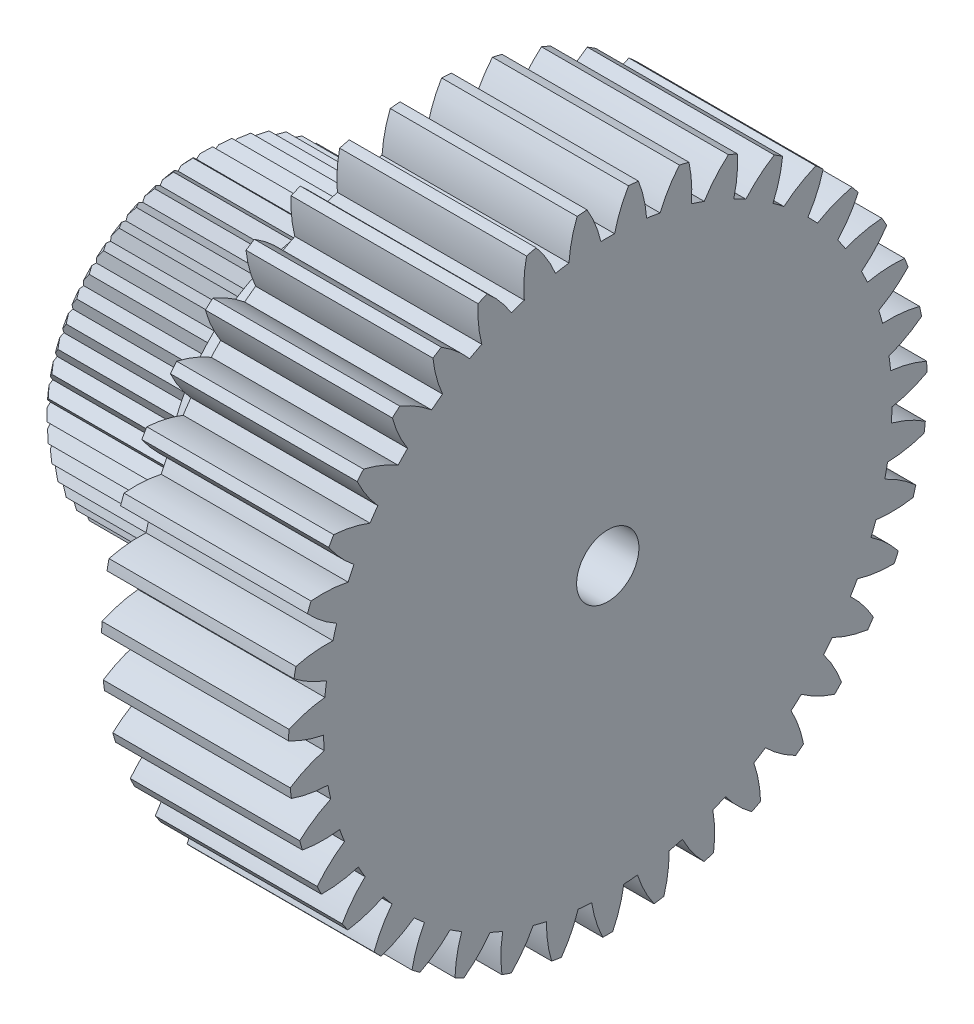
SolidWorks part; units mm, degrees
ref_plane "Plan de face" through (0, 0, 0) normal (0, 0, 1) x (1, 0, 0)
ref_plane "Plan de dessus" through (0, 0, 0) normal (0, 1, 0) x (1, 0, 0)
ref_plane "Plan de droite" through (0, 0, 0) normal (1, 0, 0) x (0, 0, -1)
ref_plane "Plan1" through (0, 0, 0) normal (0, 0, -1) x (-1, 0, 0)
sketch "Esquisse1" plane through (0, 0, 0) normal (0, 0, -1) x (-1, 0, 0)
  line L0 (-3, 5.125) -> (-3, 0)
  line L1 (-3, 0) -> (0, 0)
  line L2 (0, 0) -> (0, 5.125)
  line L3 (0, 5.125) -> (-3, 5.125)
  line L4 (-3, 0) -> (0, 0) construction
revolve "Révolution1" add sketch "Esquisse1" angle 360 about L4
sketch "Esquisse2" plane through (3, 0, 0) normal (1, 0, 0) x (0, 0, -1)
  arc A0 (1.9354, 4.7455) -> (1.3036, 4.9564) centre (0, 0) ccw
  arc A1 (1.3036, 4.9564) -> (1.3398, 4.3603) centre (-0.6017, 4.5413) cw
  arc A2 (1.3398, 4.3603) -> (1.5483, 4.2907) centre (0, 0) cw
  arc A3 (1.5483, 4.2907) -> (1.9354, 4.7455) centre (3.2092, 3.269) cw
extrude "Enlèv. mat.-Extru.1" cut sketch "Esquisse2" against normal through all
sketch "Esquisse3" plane through (3, 0, 0) normal (1, 0, 0) x (0, 0, -1)
  arc A0 (2.6716, 4.3736) -> (2.0817, 4.6832) centre (0, 0) ccw
  arc A1 (2.0817, 4.6832) -> (2.0219, 4.0889) centre (0.1345, 4.579) cw
  arc A2 (2.0219, 4.0889) -> (2.2165, 3.9868) centre (0, 0) cw
  arc A3 (2.2165, 3.9868) -> (2.6716, 4.3736) centre (3.692, 2.7119) cw
extrude "Enlèv. mat.-Extru.2" cut sketch "Esquisse3" against normal through all
sketch "Esquisse4" plane through (3, 0, 0) normal (1, 0, 0) x (0, 0, -1)
  arc A0 (3.3386, 3.8884) -> (2.806, 4.2886) centre (0, 0) ccw
  arc A1 (2.806, 4.2886) -> (2.6516, 3.7116) centre (0.8673, 4.4981) cw
  arc A2 (2.6516, 3.7116) -> (2.8273, 3.5796) centre (0, 0) cw
  arc A3 (2.8273, 3.5796) -> (3.3386, 3.8884) centre (4.0793, 2.0845) cw
extrude "Enlèv. mat.-Extru.3" cut sketch "Esquisse4" against normal through all
sketch "Esquisse5" plane through (3, 0, 0) normal (1, 0, 0) x (0, 0, -1)
  arc A0 (3.9191, 3.3025) -> (3.4576, 3.7829) centre (0, 0) ccw
  arc A1 (3.4576, 3.7829) -> (3.2127, 3.2382) centre (1.5776, 4.3008) cw
  arc A2 (3.2127, 3.2382) -> (3.3649, 3.0797) centre (0, 0) cw
  arc A3 (3.3649, 3.0797) -> (3.9191, 3.3025) centre (4.3608, 1.4032) cw
extrude "Enlèv. mat.-Extru.4" cut sketch "Esquisse5" against normal through all
sketch "Esquisse6" plane through (3, 0, 0) normal (1, 0, 0) x (0, 0, -1)
  arc A0 (4.3981, 2.6311) -> (4.0197, 3.1793) centre (0, 0) ccw
  arc A1 (4.0197, 3.1793) -> (3.6905, 2.6809) centre (2.2471, 3.992) cw
  arc A2 (3.6905, 2.6809) -> (3.8154, 2.5) centre (0, 0) cw
  arc A3 (3.8154, 2.5) -> (4.3981, 2.6311) centre (4.5294, 0.6855) cw
extrude "Enlèv. mat.-Extru.5" cut sketch "Esquisse6" against normal through all
sketch "Esquisse7" plane through (3, 0, 0) normal (1, 0, 0) x (0, 0, -1)
  arc A0 (4.7632, 1.8915) -> (4.4776, 2.4933) centre (0, 0) ccw
  arc A1 (4.4776, 2.4933) -> (4.0728, 2.0542) centre (2.8584, 3.5799) cw
  arc A2 (4.0728, 2.0542) -> (4.167, 1.8556) centre (0, 0) cw
  arc A3 (4.167, 1.8556) -> (4.7632, 1.8915) centre (4.5807, -0.05) cw
extrude "Enlèv. mat.-Extru.6" cut sketch "Esquisse7" against normal through all
sketch "Esquisse8" plane through (3, 0, 0) normal (1, 0, 0) x (0, 0, -1)
  arc A0 (5.0049, 1.1029) -> (4.8196, 1.7428) centre (0, 0) ccw
  arc A1 (4.8196, 1.7428) -> (4.3496, 1.3743) centre (3.3956, 3.075) cw
  arc A2 (4.3496, 1.3743) -> (4.4107, 1.1632) centre (0, 0) cw
  arc A3 (4.4107, 1.1632) -> (5.0049, 1.1029) centre (4.5134, -0.7841) cw
extrude "Enlèv. mat.-Extru.7" cut sketch "Esquisse8" against normal through all
sketch "Esquisse9" plane through (3, 0, 0) normal (1, 0, 0) x (0, 0, -1)
  arc A0 (5.117, 0.2858) -> (5.0367, 0.9471) centre (0, 0) ccw
  arc A1 (5.0367, 0.9471) -> (4.5137, 0.6588) centre (3.8449, 2.4905) cw
  arc A2 (4.5137, 0.6588) -> (4.5402, 0.4406) centre (0, 0) cw
  arc A3 (4.5402, 0.4406) -> (5.117, 0.2858) centre (4.3292, -1.498) cw
extrude "Enlèv. mat.-Extru.8" cut sketch "Esquisse9" against normal through all
sketch "Esquisse10" plane through (3, 0, 0) normal (1, 0, 0) x (0, 0, -1)
  arc A0 (5.0966, -0.5387) -> (5.1234, 0.1269) centre (0, 0) ccw
  arc A1 (5.1234, 0.1269) -> (4.5609, -0.0738) centre (4.1946, 1.8415) cw
  arc A2 (4.5609, -0.0738) -> (4.5521, -0.2934) centre (0, 0) cw
  arc A3 (4.5521, -0.2934) -> (5.0966, -0.5387) centre (4.0328, -2.173) cw
extrude "Enlèv. mat.-Extru.9" cut sketch "Esquisse10" against normal through all
sketch "Esquisse11" plane through (3, 0, 0) normal (1, 0, 0) x (0, 0, -1)
  arc A0 (4.9442, -1.3493) -> (5.0774, -0.6966) centre (0, 0) ccw
  arc A1 (5.0774, -0.6966) -> (4.49, -0.8045) centre (4.4357, 1.1448) cw
  arc A2 (4.49, -0.8045) -> (4.446, -1.0198) centre (0, 0) cw
  arc A3 (4.446, -1.0198) -> (4.9442, -1.3493) centre (3.632, -2.7918) cw
extrude "Enlèv. mat.-Extru.10" cut sketch "Esquisse11" against normal through all
sketch "Esquisse12" plane through (3, 0, 0) normal (1, 0, 0) x (0, 0, -1)
  arc A0 (4.6637, -2.1249) -> (4.8999, -1.5021) centre (0, 0) ccw
  arc A1 (4.8999, -1.5021) -> (4.3028, -1.5143) centre (4.5619, 0.4184) cw
  arc A2 (4.3028, -1.5143) -> (4.2249, -1.7198) centre (0, 0) cw
  arc A3 (4.2249, -1.7198) -> (4.6637, -2.1249) centre (3.1371, -3.3382) cw
extrude "Enlèv. mat.-Extru.11" cut sketch "Esquisse12" against normal through all
sketch "Esquisse13" plane through (3, 0, 0) normal (1, 0, 0) x (0, 0, -1)
  arc A0 (4.2625, -2.8455) -> (4.5955, -2.2686) centre (0, 0) ccw
  arc A1 (4.5955, -2.2686) -> (4.0042, -2.1849) centre (4.5699, -0.3188) cw
  arc A2 (4.0042, -2.1849) -> (3.8943, -2.3753) centre (0, 0) cw
  arc A3 (3.8943, -2.3753) -> (4.2625, -2.8455) centre (2.561, -3.7982) cw
extrude "Enlèv. mat.-Extru.12" cut sketch "Esquisse13" against normal through all
sketch "Esquisse14" plane through (3, 0, 0) normal (1, 0, 0) x (0, 0, -1)
  arc A0 (3.7508, -3.4924) -> (4.1721, -2.9764) centre (0, 0) ccw
  arc A1 (4.1721, -2.9764) -> (3.6018, -2.7989) centre (4.4596, -1.0477) cw
  arc A2 (3.6018, -2.7989) -> (3.4628, -2.9692) centre (0, 0) cw
  arc A3 (3.4628, -2.9692) -> (3.7508, -3.4924) centre (1.9186, -4.1599) cw
extrude "Enlèv. mat.-Extru.13" cut sketch "Esquisse14" against normal through all
sketch "Esquisse15" plane through (3, 0, 0) normal (1, 0, 0) x (0, 0, -1)
  arc A0 (3.142, -4.0489) -> (3.6406, -3.6071) centre (0, 0) ccw
  arc A1 (3.6406, -3.6071) -> (3.1062, -3.3405) centre (4.2338, -1.7495) cw
  arc A2 (3.1062, -3.3405) -> (2.9417, -3.4862) centre (0, 0) cw
  arc A3 (2.9417, -3.4862) -> (3.142, -4.0489) centre (1.2264, -4.4138) cw
extrude "Enlèv. mat.-Extru.14" cut sketch "Esquisse15" against normal through all
sketch "Esquisse16" plane through (3, 0, 0) normal (1, 0, 0) x (0, 0, -1)
  arc A0 (2.4518, -4.5005) -> (3.0149, -4.1444) centre (0, 0) ccw
  arc A1 (3.0149, -4.1444) -> (2.5301, -3.7955) centre (3.8983, -2.406) cw
  arc A2 (2.5301, -3.7955) -> (2.3444, -3.9129) centre (0, 0) cw
  arc A3 (2.3444, -3.9129) -> (2.4518, -4.5005) centre (0.5025, -4.5534) cw
extrude "Enlèv. mat.-Extru.15" cut sketch "Esquisse16" against normal through all
sketch "Esquisse17" plane through (3, 0, 0) normal (1, 0, 0) x (0, 0, -1)
  arc A0 (1.6982, -4.8355) -> (2.311, -4.5744) centre (0, 0) ccw
  arc A1 (2.311, -4.5744) -> (1.8885, -4.1522) centre (3.4619, -3.0002) cw
  arc A2 (1.8885, -4.1522) -> (1.6863, -4.2383) centre (0, 0) cw
  arc A3 (1.6863, -4.2383) -> (1.6982, -4.8355) centre (-0.2344, -4.575) cw
extrude "Enlèv. mat.-Extru.16" cut sketch "Esquisse17" against normal through all
sketch "Esquisse18" plane through (3, 0, 0) normal (1, 0, 0) x (0, 0, -1)
  arc A0 (0.9005, -5.0453) -> (1.5473, -4.8858) centre (0, 0) ccw
  arc A1 (1.5473, -4.8858) -> (1.198, -4.4014) centre (2.9358, -3.5167) cw
  arc A2 (1.198, -4.4014) -> (0.9846, -4.454) centre (0, 0) cw
  arc A3 (0.9846, -4.454) -> (0.9005, -5.0453) centre (-0.9652, -4.4782) cw
extrude "Enlèv. mat.-Extru.17" cut sketch "Esquisse18" against normal through all
sketch "Esquisse19" plane through (3, 0, 0) normal (1, 0, 0) x (0, 0, -1)
  arc A0 (0.0795, -5.1244) -> (0.7435, -5.0708) centre (0, 0) ccw
  arc A1 (0.7435, -5.0708) -> (0.4765, -4.5365) centre (2.3336, -3.942) cw
  arc A2 (0.4765, -4.5365) -> (0.2574, -4.5542) centre (0, 0) cw
  arc A3 (0.2574, -4.5542) -> (0.0795, -5.1244) centre (-1.6711, -4.2653) cw
extrude "Enlèv. mat.-Extru.18" cut sketch "Esquisse19" against normal through all
sketch "Esquisse20" plane through (3, 0, 0) normal (1, 0, 0) x (0, 0, -1)
  arc A0 (-0.7435, -5.0708) -> (-0.0795, -5.1244) centre (0, 0) ccw
  arc A1 (-0.0795, -5.1244) -> (-0.2574, -4.5542) centre (1.6711, -4.2653) cw
  arc A2 (-0.2574, -4.5542) -> (-0.4765, -4.5365) centre (0, 0) cw
  arc A3 (-0.4765, -4.5365) -> (-0.7435, -5.0708) centre (-2.3336, -3.942) cw
extrude "Enlèv. mat.-Extru.19" cut sketch "Esquisse20" against normal through all
sketch "Esquisse21" plane through (3, 0, 0) normal (1, 0, 0) x (0, 0, -1)
  arc A0 (-1.5473, -4.8858) -> (-0.9005, -5.0453) centre (0, 0) ccw
  arc A1 (-0.9005, -5.0453) -> (-0.9846, -4.454) centre (0.9652, -4.4782) cw
  arc A2 (-0.9846, -4.454) -> (-1.198, -4.4014) centre (0, 0) cw
  arc A3 (-1.198, -4.4014) -> (-1.5473, -4.8858) centre (-2.9358, -3.5167) cw
extrude "Enlèv. mat.-Extru.20" cut sketch "Esquisse21" against normal through all
sketch "Esquisse22" plane through (3, 0, 0) normal (1, 0, 0) x (0, 0, -1)
  arc A0 (-2.311, -4.5744) -> (-1.6982, -4.8355) centre (0, 0) ccw
  arc A1 (-1.6982, -4.8355) -> (-1.6863, -4.2383) centre (0.2344, -4.575) cw
  arc A2 (-1.6863, -4.2383) -> (-1.8885, -4.1522) centre (0, 0) cw
  arc A3 (-1.8885, -4.1522) -> (-2.311, -4.5744) centre (-3.4619, -3.0002) cw
extrude "Enlèv. mat.-Extru.21" cut sketch "Esquisse22" against normal through all
sketch "Esquisse23" plane through (3, 0, 0) normal (1, 0, 0) x (0, 0, -1)
  arc A0 (-3.0149, -4.1444) -> (-2.4518, -4.5005) centre (0, 0) ccw
  arc A1 (-2.4518, -4.5005) -> (-2.3444, -3.9129) centre (-0.5025, -4.5534) cw
  arc A2 (-2.3444, -3.9129) -> (-2.5301, -3.7955) centre (0, 0) cw
  arc A3 (-2.5301, -3.7955) -> (-3.0149, -4.1444) centre (-3.8983, -2.406) cw
extrude "Enlèv. mat.-Extru.22" cut sketch "Esquisse23" against normal through all
sketch "Esquisse24" plane through (3, 0, 0) normal (1, 0, 0) x (0, 0, -1)
  arc A0 (-3.6406, -3.6071) -> (-3.142, -4.0489) centre (0, 0) ccw
  arc A1 (-3.142, -4.0489) -> (-2.9417, -3.4862) centre (-1.2264, -4.4138) cw
  arc A2 (-2.9417, -3.4862) -> (-3.1062, -3.3405) centre (0, 0) cw
  arc A3 (-3.1062, -3.3405) -> (-3.6406, -3.6071) centre (-4.2338, -1.7495) cw
extrude "Enlèv. mat.-Extru.23" cut sketch "Esquisse24" against normal through all
sketch "Esquisse25" plane through (3, 0, 0) normal (1, 0, 0) x (0, 0, -1)
  arc A0 (-4.1721, -2.9764) -> (-3.7508, -3.4924) centre (0, 0) ccw
  arc A1 (-3.7508, -3.4924) -> (-3.4628, -2.9692) centre (-1.9186, -4.1599) cw
  arc A2 (-3.4628, -2.9692) -> (-3.6018, -2.7989) centre (0, 0) cw
  arc A3 (-3.6018, -2.7989) -> (-4.1721, -2.9764) centre (-4.4596, -1.0477) cw
extrude "Enlèv. mat.-Extru.24" cut sketch "Esquisse25" against normal through all
sketch "Esquisse26" plane through (3, 0, 0) normal (1, 0, 0) x (0, 0, -1)
  arc A0 (-4.5955, -2.2686) -> (-4.2625, -2.8455) centre (0, 0) ccw
  arc A1 (-4.2625, -2.8455) -> (-3.8943, -2.3753) centre (-2.561, -3.7982) cw
  arc A2 (-3.8943, -2.3753) -> (-4.0042, -2.1849) centre (0, 0) cw
  arc A3 (-4.0042, -2.1849) -> (-4.5955, -2.2686) centre (-4.5699, -0.3188) cw
extrude "Enlèv. mat.-Extru.25" cut sketch "Esquisse26" against normal through all
sketch "Esquisse27" plane through (3, 0, 0) normal (1, 0, 0) x (0, 0, -1)
  arc A0 (-4.8999, -1.5021) -> (-4.6637, -2.1249) centre (0, 0) ccw
  arc A1 (-4.6637, -2.1249) -> (-4.2249, -1.7198) centre (-3.1371, -3.3382) cw
  arc A2 (-4.2249, -1.7198) -> (-4.3028, -1.5143) centre (0, 0) cw
  arc A3 (-4.3028, -1.5143) -> (-4.8999, -1.5021) centre (-4.5619, 0.4184) cw
extrude "Enlèv. mat.-Extru.26" cut sketch "Esquisse27" against normal through all
sketch "Esquisse28" plane through (3, 0, 0) normal (1, 0, 0) x (0, 0, -1)
  arc A0 (-5.0774, -0.6966) -> (-4.9442, -1.3493) centre (0, 0) ccw
  arc A1 (-4.9442, -1.3493) -> (-4.446, -1.0198) centre (-3.632, -2.7918) cw
  arc A2 (-4.446, -1.0198) -> (-4.49, -0.8045) centre (0, 0) cw
  arc A3 (-4.49, -0.8045) -> (-5.0774, -0.6966) centre (-4.4357, 1.1448) cw
extrude "Enlèv. mat.-Extru.27" cut sketch "Esquisse28" against normal through all
sketch "Esquisse29" plane through (3, 0, 0) normal (1, 0, 0) x (0, 0, -1)
  arc A0 (-5.1234, 0.1269) -> (-5.0966, -0.5387) centre (0, 0) ccw
  arc A1 (-5.0966, -0.5387) -> (-4.5521, -0.2934) centre (-4.0328, -2.173) cw
  arc A2 (-4.5521, -0.2934) -> (-4.5609, -0.0738) centre (0, 0) cw
  arc A3 (-4.5609, -0.0738) -> (-5.1234, 0.1269) centre (-4.1946, 1.8415) cw
extrude "Enlèv. mat.-Extru.28" cut sketch "Esquisse29" against normal through all
sketch "Esquisse30" plane through (3, 0, 0) normal (1, 0, 0) x (0, 0, -1)
  arc A0 (-5.0367, 0.9471) -> (-5.117, 0.2858) centre (0, 0) ccw
  arc A1 (-5.117, 0.2858) -> (-4.5402, 0.4406) centre (-4.3292, -1.498) cw
  arc A2 (-4.5402, 0.4406) -> (-4.5137, 0.6588) centre (0, 0) cw
  arc A3 (-4.5137, 0.6588) -> (-5.0367, 0.9471) centre (-3.8449, 2.4905) cw
extrude "Enlèv. mat.-Extru.29" cut sketch "Esquisse30" against normal through all
sketch "Esquisse31" plane through (3, 0, 0) normal (1, 0, 0) x (0, 0, -1)
  arc A0 (-4.8196, 1.7428) -> (-5.0049, 1.1029) centre (0, 0) ccw
  arc A1 (-5.0049, 1.1029) -> (-4.4107, 1.1632) centre (-4.5134, -0.7841) cw
  arc A2 (-4.4107, 1.1632) -> (-4.3496, 1.3743) centre (0, 0) cw
  arc A3 (-4.3496, 1.3743) -> (-4.8196, 1.7428) centre (-3.3956, 3.075) cw
extrude "Enlèv. mat.-Extru.30" cut sketch "Esquisse31" against normal through all
sketch "Esquisse32" plane through (3, 0, 0) normal (1, 0, 0) x (0, 0, -1)
  arc A0 (-4.4776, 2.4933) -> (-4.7632, 1.8915) centre (0, 0) ccw
  arc A1 (-4.7632, 1.8915) -> (-4.167, 1.8556) centre (-4.5807, -0.05) cw
  arc A2 (-4.167, 1.8556) -> (-4.0728, 2.0542) centre (0, 0) cw
  arc A3 (-4.0728, 2.0542) -> (-4.4776, 2.4933) centre (-2.8584, 3.5799) cw
extrude "Enlèv. mat.-Extru.31" cut sketch "Esquisse32" against normal through all
sketch "Esquisse33" plane through (3, 0, 0) normal (1, 0, 0) x (0, 0, -1)
  arc A0 (-4.0197, 3.1793) -> (-4.3981, 2.6311) centre (0, 0) ccw
  arc A1 (-4.3981, 2.6311) -> (-3.8154, 2.5) centre (-4.5294, 0.6855) cw
  arc A2 (-3.8154, 2.5) -> (-3.6905, 2.6809) centre (0, 0) cw
  arc A3 (-3.6905, 2.6809) -> (-4.0197, 3.1793) centre (-2.2471, 3.992) cw
extrude "Enlèv. mat.-Extru.32" cut sketch "Esquisse33" against normal through all
sketch "Esquisse34" plane through (3, 0, 0) normal (1, 0, 0) x (0, 0, -1)
  arc A0 (-3.4576, 3.7829) -> (-3.9191, 3.3025) centre (0, 0) ccw
  arc A1 (-3.9191, 3.3025) -> (-3.3649, 3.0797) centre (-4.3608, 1.4032) cw
  arc A2 (-3.3649, 3.0797) -> (-3.2127, 3.2382) centre (0, 0) cw
  arc A3 (-3.2127, 3.2382) -> (-3.4576, 3.7829) centre (-1.5776, 4.3008) cw
extrude "Enlèv. mat.-Extru.33" cut sketch "Esquisse34" against normal through all
sketch "Esquisse35" plane through (3, 0, 0) normal (1, 0, 0) x (0, 0, -1)
  arc A0 (-2.806, 4.2886) -> (-3.3386, 3.8884) centre (0, 0) ccw
  arc A1 (-3.3386, 3.8884) -> (-2.8273, 3.5796) centre (-4.0793, 2.0845) cw
  arc A2 (-2.8273, 3.5796) -> (-2.6516, 3.7116) centre (0, 0) cw
  arc A3 (-2.6516, 3.7116) -> (-2.806, 4.2886) centre (-0.8673, 4.4981) cw
extrude "Enlèv. mat.-Extru.34" cut sketch "Esquisse35" against normal through all
sketch "Esquisse36" plane through (3, 0, 0) normal (1, 0, 0) x (0, 0, -1)
  arc A0 (-2.0817, 4.6832) -> (-2.6716, 4.3736) centre (0, 0) ccw
  arc A1 (-2.6716, 4.3736) -> (-2.2165, 3.9868) centre (-3.692, 2.7119) cw
  arc A2 (-2.2165, 3.9868) -> (-2.0219, 4.0889) centre (0, 0) cw
  arc A3 (-2.0219, 4.0889) -> (-2.0817, 4.6832) centre (-0.1345, 4.579) cw
extrude "Enlèv. mat.-Extru.35" cut sketch "Esquisse36" against normal through all
sketch "Esquisse37" plane through (3, 0, 0) normal (1, 0, 0) x (0, 0, -1)
  arc A0 (-1.3036, 4.9564) -> (-1.9354, 4.7455) centre (0, 0) ccw
  arc A1 (-1.9354, 4.7455) -> (-1.5483, 4.2907) centre (-3.2092, 3.269) cw
  arc A2 (-1.5483, 4.2907) -> (-1.3398, 4.3603) centre (0, 0) cw
  arc A3 (-1.3398, 4.3603) -> (-1.3036, 4.9564) centre (0.6017, 4.5413) cw
extrude "Enlèv. mat.-Extru.36" cut sketch "Esquisse37" against normal through all
sketch "Esquisse38" plane through (3, 0, 0) normal (1, 0, 0) x (0, 0, -1)
  arc A0 (-0.4916, 5.1014) -> (-1.1491, 4.9945) centre (0, 0) ccw
  arc A1 (-1.1491, 4.9945) -> (-0.84, 4.4835) centre (-2.6433, 3.7415) cw
  arc A2 (-0.84, 4.4835) -> (-0.623, 4.5187) centre (0, 0) cw
  arc A3 (-0.623, 4.5187) -> (-0.4916, 5.1014) centre (1.3224, 4.386) cw
extrude "Enlèv. mat.-Extru.37" cut sketch "Esquisse38" against normal through all
sketch "Esquisse39" plane through (3, 0, 0) normal (1, 0, 0) x (0, 0, -1)
  arc A0 (0.3331, 5.1142) -> (-0.3331, 5.1142) centre (0, 0) ccw
  arc A1 (-0.3331, 5.1142) -> (-0.1099, 4.5602) centre (-2.0089, 4.117) cw
  arc A2 (-0.1099, 4.5602) -> (0.1099, 4.5602) centre (0, 0) cw
  arc A3 (0.1099, 4.5602) -> (0.3331, 5.1142) centre (2.0089, 4.117) cw
extrude "Enlèv. mat.-Extru.38" cut sketch "Esquisse39" against normal through all
sketch "Esquisse40" plane through (3, 0, 0) normal (1, 0, 0) x (0, 0, -1)
  arc A0 (1.1491, 4.9945) -> (0.4916, 5.1014) centre (0, 0) ccw
  arc A1 (0.4916, 5.1014) -> (0.623, 4.5187) centre (-1.3224, 4.386) cw
  arc A2 (0.623, 4.5187) -> (0.84, 4.4835) centre (0, 0) cw
  arc A3 (0.84, 4.4835) -> (1.1491, 4.9945) centre (2.6433, 3.7415) cw
extrude "Enlèv. mat.-Extru.39" cut sketch "Esquisse40" against normal through all
hole_wizard "Diamètre du perçage Ø7.0 (7)1" positions "Esquisse42" profile "Esquisse41" hole size "Ø7.0" standard "Ansi Metric"
sketch "Esquisse42" plane through (0, 0, 0) normal (-1, 0, 0) x (0, 0, 1)
  point P0 (0, 0)
sketch "Esquisse41" plane through (0, 0, 0) normal (0, 1, 0) x (0, 0, 1)
  line L0 (0, 0) -> (0, 1)
  line L1 (0, 1) -> (3.5, 1)
  line L2 (3.5, 1) -> (3.5, 0)
  line L5 (3.5, 0) -> (0, 0)
  line L10 (0, 1) -> (-3.5, 1) construction
  line L11 (0, -6.35) -> (0, 107.95) construction
  dimension "Diamètre du perçage" = 7
  dimension "Profondeur du perçage" = 1
  dimension "Angle de pointe" = 180
sketch "Esquisse43" plane through (0, 0, 0) normal (0, 0, 1) x (1, 0, 0)
  line L0 (-3.0001, 2.5) -> (-3.0001, 0)
  line L1 (-3.0001, 0) -> (1, 0)
  line L2 (1, 0) -> (1, 2.5)
  line L3 (1, 2.5) -> (-3.0001, 2.5)
  line L4 (-3.0001, 0) -> (1, 0) construction
revolve "Révolution2" add sketch "Esquisse43" angle 360 about L4
hole_wizard "Diamètre du perçage Ø1.0 (1)1" positions "Esquisse45" profile "Esquisse44" hole size "Ø1.0" standard "Ansi Metric"
sketch "Esquisse45" plane through (3, 0, 0) normal (1, 0, 0) x (0, 0, -1)
  point P0 (0, 0)
sketch "Esquisse44" plane through (3, 0, 0) normal (0, 1, 0) x (0, 0, -1)
  line L0 (0, 0) -> (0, 6.0001)
  line L1 (0, 6.0001) -> (0.5, 6.0001)
  line L2 (0.5, 6.0001) -> (0.5, 0)
  line L5 (0.5, 0) -> (0, 0)
  line L11 (0, -6.35) -> (0, 107.95) construction
  dimension "Diamètre du perçage jusqu'au prochain" = 1
  dimension "Profondeur du perçage jusqu'au prochain" = 6.0001
sketch "Esquisse46" plane through (-3.0001, 0, 0) normal (-1, 0, 0) x (0, 0, 1)
  circle A0 centre (0, 0) radius 0.5 construction
  circle A1 centre (0, 0) radius 2.5
  circle A2 centre (0, 0) radius 2.5
  circle A3 centre (0, 0) radius 0.5
  dimension "D1" = 0
extrude "Boss.-Extru.1" add sketch "Esquisse46" along normal blind 0.6
chamfer "Chanfrein1" distance 0.1 angle 45 1 edges at (-3.6001, 0, 2.5)
sketch "Esquisse47" plane through (-3.6001, 0, 0) normal (-1, 0, 0) x (0, 0, 1)
  line L0 (0, 0) -> (0, 3.1941) construction
  line L1 (-0.157, 2.4951) -> (0, 2.35)
  line L2 (0.1955, 3.1082) -> (0, 0) construction
  line L3 (0, 0) -> (-0.186, 2.9567) construction
  line L4 (0, 2.35) -> (0.157, 2.4951)
  line L5 (0.157, 2.4951) -> (0.2945, 2.3315)
  line L6 (0.2945, 2.3315) -> (0.4685, 2.4557)
  line L7 (0.4685, 2.4557) -> (0.5844, 2.2762)
  line L8 (0.5844, 2.2762) -> (0.7725, 2.3776)
  line L9 (0.7725, 2.3776) -> (0.8651, 2.185)
  line L10 (0.8651, 2.185) -> (1.0644, 2.2621)
  line L11 (1.0644, 2.2621) -> (1.1321, 2.0593)
  line L12 (1.1321, 2.0593) -> (1.3396, 2.1108)
  line L13 (1.3396, 2.1108) -> (1.3813, 1.9012)
  line L14 (1.3813, 1.9012) -> (1.5936, 1.9263)
  line L15 (1.5936, 1.9263) -> (1.6087, 1.7131)
  line L16 (1.6087, 1.7131) -> (1.8224, 1.7114)
  line L17 (1.8224, 1.7114) -> (1.8107, 1.4979)
  line L18 (1.8107, 1.4979) -> (2.0225, 1.4695)
  line L19 (2.0225, 1.4695) -> (1.9842, 1.2592)
  line L20 (1.9842, 1.2592) -> (2.1908, 1.2044)
  line L21 (2.1908, 1.2044) -> (2.1263, 1.0006)
  line L22 (2.1263, 1.0006) -> (2.3244, 0.9203)
  line L23 (2.3244, 0.9203) -> (2.235, 0.7262)
  line L24 (2.235, 0.7262) -> (2.4215, 0.6217)
  line L25 (2.4215, 0.6217) -> (2.3084, 0.4403)
  line L26 (2.3084, 0.4403) -> (2.4803, 0.3133)
  line L27 (2.4803, 0.3133) -> (2.3454, 0.1476)
  line L28 (2.3454, 0.1476) -> (2.5, 0)
  line L29 (2.5, 0) -> (2.3454, -0.1476)
  line L30 (2.3454, -0.1476) -> (2.4803, -0.3133)
  line L31 (2.4803, -0.3133) -> (2.3084, -0.4403)
  line L32 (2.3084, -0.4403) -> (2.4215, -0.6217)
  line L33 (2.4215, -0.6217) -> (2.235, -0.7262)
  line L34 (2.235, -0.7262) -> (2.3244, -0.9203)
  line L35 (2.3244, -0.9203) -> (2.1263, -1.0006)
  line L36 (2.1263, -1.0006) -> (2.1908, -1.2044)
  line L37 (2.1908, -1.2044) -> (1.9842, -1.2592)
  line L38 (1.9842, -1.2592) -> (2.0225, -1.4695)
  line L39 (2.0225, -1.4695) -> (1.8107, -1.4979)
  line L40 (1.8107, -1.4979) -> (1.8224, -1.7114)
  line L41 (1.8224, -1.7114) -> (1.6087, -1.7131)
  line L42 (1.6087, -1.7131) -> (1.5936, -1.9263)
  line L43 (1.5936, -1.9263) -> (1.3813, -1.9012)
  line L44 (1.3813, -1.9012) -> (1.3396, -2.1108)
  line L45 (1.3396, -2.1108) -> (1.1321, -2.0593)
  line L46 (1.1321, -2.0593) -> (1.0644, -2.2621)
  line L47 (1.0644, -2.2621) -> (0.8651, -2.185)
  line L48 (0.8651, -2.185) -> (0.7725, -2.3776)
  line L49 (0.7725, -2.3776) -> (0.5844, -2.2762)
  line L50 (0.5844, -2.2762) -> (0.4685, -2.4557)
  line L51 (0.4685, -2.4557) -> (0.2945, -2.3315)
  line L52 (0.2945, -2.3315) -> (0.157, -2.4951)
  line L53 (0.157, -2.4951) -> (0, -2.35)
  line L54 (0, -2.35) -> (-0.157, -2.4951)
  line L55 (-0.157, -2.4951) -> (-0.2945, -2.3315)
  line L56 (-0.2945, -2.3315) -> (-0.4685, -2.4557)
  line L57 (-0.4685, -2.4557) -> (-0.5844, -2.2762)
  line L58 (-0.5844, -2.2762) -> (-0.7725, -2.3776)
  line L59 (-0.7725, -2.3776) -> (-0.8651, -2.185)
  line L60 (-0.8651, -2.185) -> (-1.0644, -2.2621)
  line L61 (-1.0644, -2.2621) -> (-1.1321, -2.0593)
  line L62 (-1.1321, -2.0593) -> (-1.3396, -2.1108)
  line L63 (-1.3396, -2.1108) -> (-1.3813, -1.9012)
  line L64 (-1.3813, -1.9012) -> (-1.5936, -1.9263)
  line L65 (-1.5936, -1.9263) -> (-1.6087, -1.7131)
  line L66 (-1.6087, -1.7131) -> (-1.8224, -1.7114)
  line L67 (-1.8224, -1.7114) -> (-1.8107, -1.4979)
  line L68 (-1.8107, -1.4979) -> (-2.0225, -1.4695)
  line L69 (-2.0225, -1.4695) -> (-1.9842, -1.2592)
  line L70 (-1.9842, -1.2592) -> (-2.1908, -1.2044)
  line L71 (-2.1908, -1.2044) -> (-2.1263, -1.0006)
  line L72 (-2.1263, -1.0006) -> (-2.3244, -0.9203)
  line L73 (-2.3244, -0.9203) -> (-2.235, -0.7262)
  line L74 (-2.235, -0.7262) -> (-2.4215, -0.6217)
  line L75 (-2.4215, -0.6217) -> (-2.3084, -0.4403)
  line L76 (-2.3084, -0.4403) -> (-2.4803, -0.3133)
  line L77 (-2.4803, -0.3133) -> (-2.3454, -0.1476)
  line L78 (-2.3454, -0.1476) -> (-2.5, 0)
  line L79 (-2.5, 0) -> (-2.3454, 0.1476)
  line L80 (-2.3454, 0.1476) -> (-2.4803, 0.3133)
  line L81 (-2.4803, 0.3133) -> (-2.3084, 0.4403)
  line L82 (-2.3084, 0.4403) -> (-2.4215, 0.6217)
  line L83 (-2.4215, 0.6217) -> (-2.235, 0.7262)
  line L84 (-2.235, 0.7262) -> (-2.3244, 0.9203)
  line L85 (-2.3244, 0.9203) -> (-2.1263, 1.0006)
  line L86 (-2.1263, 1.0006) -> (-2.1908, 1.2044)
  line L87 (-2.1908, 1.2044) -> (-1.9842, 1.2592)
  line L88 (-1.9842, 1.2592) -> (-2.0225, 1.4695)
  line L89 (-2.0225, 1.4695) -> (-1.8107, 1.4979)
  line L90 (-1.8107, 1.4979) -> (-1.8224, 1.7114)
  line L91 (-1.8224, 1.7114) -> (-1.6087, 1.7131)
  line L92 (-1.6087, 1.7131) -> (-1.5936, 1.9263)
  line L93 (-1.5936, 1.9263) -> (-1.3813, 1.9012)
  line L94 (-1.3813, 1.9012) -> (-1.3396, 2.1108)
  line L95 (-1.3396, 2.1108) -> (-1.1321, 2.0593)
  line L96 (-1.1321, 2.0593) -> (-1.0644, 2.2621)
  line L97 (-1.0644, 2.2621) -> (-0.8651, 2.185)
  line L98 (-0.8651, 2.185) -> (-0.7725, 2.3776)
  line L99 (-0.7725, 2.3776) -> (-0.5844, 2.2762)
  line L100 (-0.5844, 2.2762) -> (-0.4685, 2.4557)
  line L101 (-0.4685, 2.4557) -> (-0.2945, 2.3315)
  line L102 (-0.2945, 2.3315) -> (-0.157, 2.4951)
  circle A0 centre (0, 0) radius 2.35 construction
  circle A1 centre (0, 0) radius 2.5 construction
  circle A2 centre (0, 0) radius 3.1485
  point P160 (0, 0)
  dimension "D1" = 4.7
  dimension "D4" = 50
  dimension "D2" = 3.6
  dimension "D3" = 3.6
extrude "Enlèv. mat.-Extru.40" cut sketch "Esquisse47" against normal blind 2
